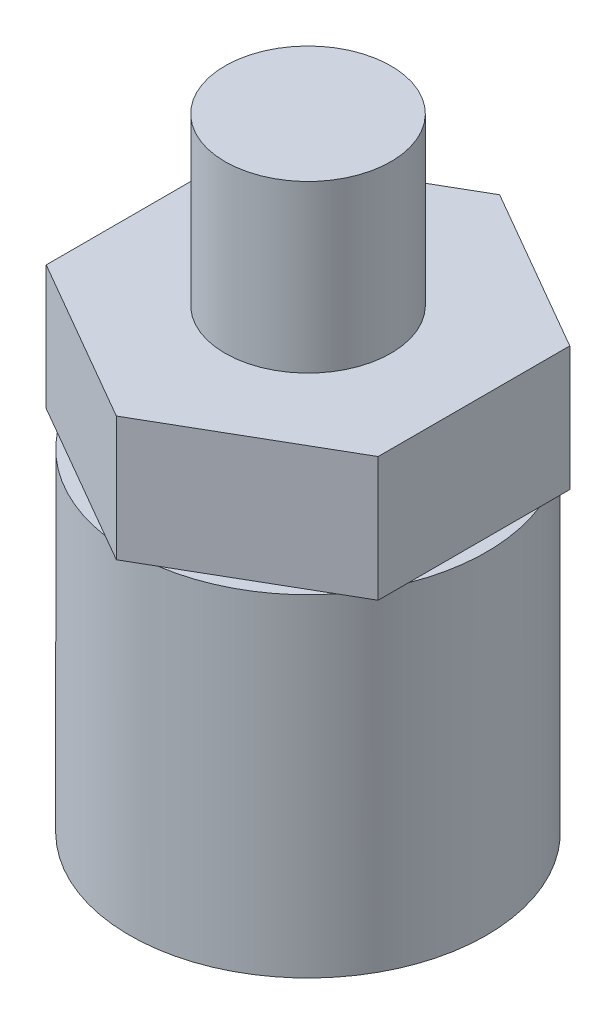
SolidWorks part; units mm, degrees
ref_plane "Front Plane" through (0, 0, 0) normal (0, 0, 1) x (1, 0, 0)
ref_plane "Top Plane" through (0, 0, 0) normal (0, 1, 0) x (1, 0, 0)
ref_plane "Right Plane" through (0, 0, 0) normal (1, 0, 0) x (0, 0, -1)
sketch "Sketch1" plane through (0, 0, 0) normal (0, 1, 0) x (1, 0, 0)
  line L1 (0, -4.6188) -> (4, -2.3094)
  line L2 (4, -2.3094) -> (4, 2.3094)
  line L3 (4, 2.3094) -> (0, 4.6188)
  line L4 (0, 4.6188) -> (-4, 2.3094)
  line L5 (-4, 2.3094) -> (-4, -2.3094)
  line L6 (-4, -2.3094) -> (0, -4.6188)
  circle A0 centre (0, 0) radius 4 construction
  dimension "D1" = 8
extrude "Boss-Extrude1" add sketch "Sketch1" along normal blind 3
sketch "Sketch2" plane through (0, 0, 0) normal (0, -1, 0) x (1, 0, 0)
  circle A0 centre (0, 0) radius 4.3
  dimension "D1" = 8.6
extrude "Boss-Extrude2" add sketch "Sketch2" along normal blind 8
sketch "Sketch3" plane through (0, 3, 0) normal (0, 1, 0) x (1, 0, 0)
  circle A0 centre (0, 0) radius 2
  dimension "D1" = 4
extrude "Boss-Extrude3" add sketch "Sketch3" along normal blind 4
